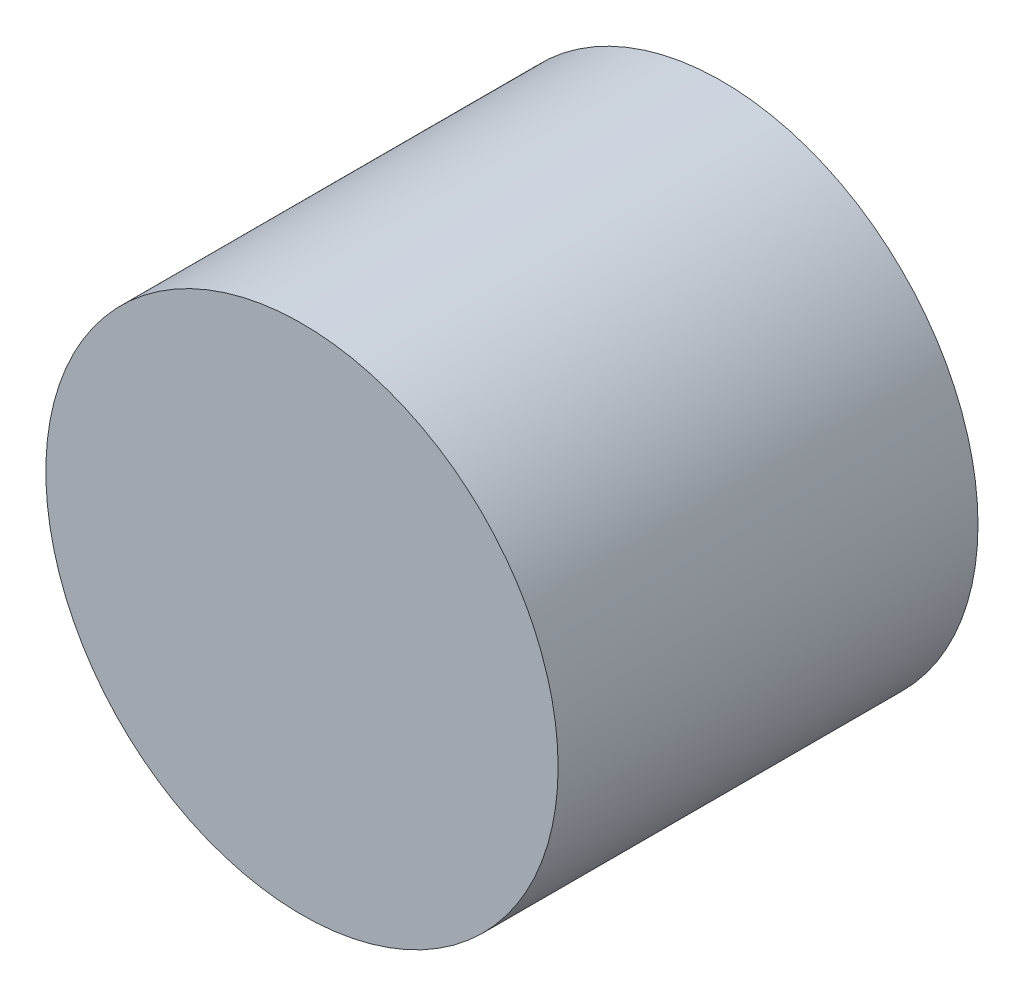
SolidWorks part; units mm, degrees
ref_plane "Front Plane" through (0, 0, 0) normal (0, 0, 1) x (1, 0, 0)
ref_plane "Top Plane" through (0, 0, 0) normal (0, 1, 0) x (1, 0, 0)
ref_plane "Right Plane" through (0, 0, 0) normal (1, 0, 0) x (0, 0, -1)
sketch "Sketch1" plane through (0, 0, 0) normal (0, 0, 1) x (1, 0, 0)
  circle A0 centre (0, 0) radius 6.1
  dimension "D1" = 12.2
extrude "Boss-Extrude1" add sketch "Sketch1" along normal blind 10
